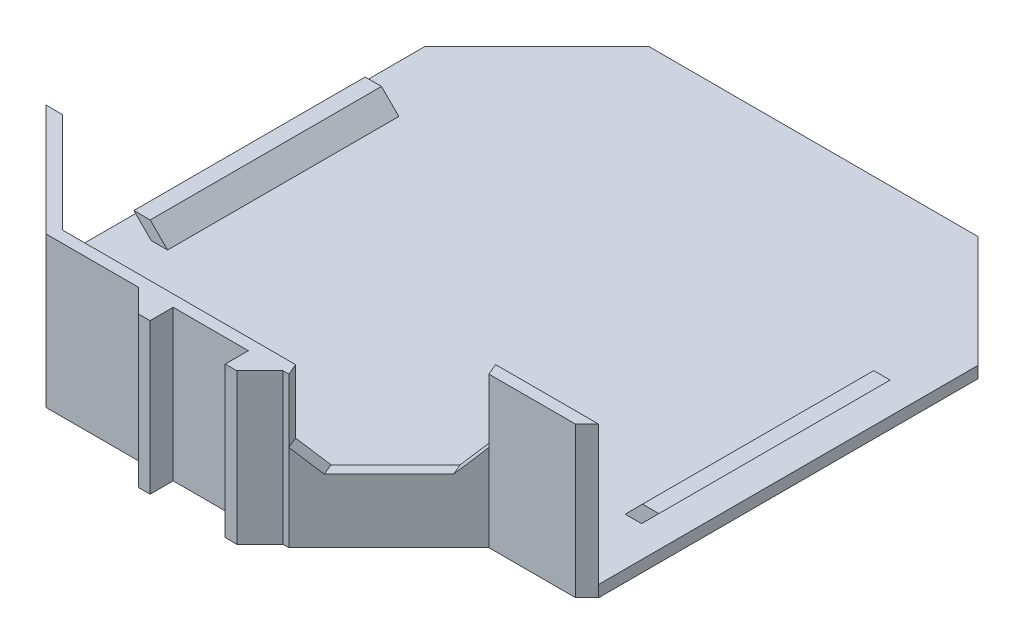
SolidWorks part; units mm, degrees
ref_plane "Front Plane" through (0, 0, 0) normal (0, 0, 1) x (1, 0, 0)
ref_plane "Top Plane" through (0, 0, 0) normal (0, 1, 0) x (1, 0, 0)
ref_plane "Right Plane" through (0, 0, 0) normal (1, 0, 0) x (0, 0, -1)
sketch "Sketch1" plane through (0, 0, 0) normal (0, 1, 0) x (1, 0, 0)
  line L0 (-1145.7751, 0) -> (48854.2249, 0) construction
  line L1 (0, -935.409) -> (0, 49064.591) construction
  line L2 (-36.195, 66.167) -> (36.195, 66.167)
  line L3 (36.195, 66.167) -> (60.706, 41.656)
  line L4 (60.706, 41.656) -> (60.706, -41.656)
  line L5 (-60.706, 41.656) -> (-60.706, -41.656)
  line L6 (-36.195, 66.167) -> (-60.706, 41.656)
  line L7 (-36.195, -66.167) -> (-60.706, -41.656)
  line L8 (-36.195, -66.167) -> (36.195, -66.167)
  line L9 (36.195, -66.167) -> (60.706, -41.656)
  point P10 (0, 66.167)
  point P11 (-60.706, 0)
  point P14 (60.706, 0)
  dimension "D1" = 132.334
  dimension "D2" = 121.412
  dimension "D3" = 135
  dimension "D4" = 41.656
extrude "Boss-Extrude1" add sketch "Sketch1" along normal blind 2.54
sketch "Sketch5" plane through (0, 2.54, 0) normal (0, 1, 0) x (1, 0, 0)
  line L0 (58.166, -44.196) -> (36.195, -66.167)
  line L1 (36.195, -66.167) -> (60.706, -41.656) construction
  line L2 (36.195, -66.167) -> (17.145, -66.167)
  line L3 (-36.195, -66.167) -> (36.195, -66.167) construction
  line L4 (17.145, -66.167) -> (39.116, -44.196)
  line L5 (39.116, -44.196) -> (58.166, -44.196)
  dimension "D1" = 19.05
  dimension "D2" = 2.54
extrude "Cut-Extrude1" cut sketch "Sketch5" against normal through all
sketch "Case Reference" plane through (0, 0, 0) normal (0, 0, 1) x (1, 0, 0)
  line L0 (-60.706, 2.54) -> (-60.706, 13.97) construction
  line L1 (-60.706, 13.97) -> (-58.166, 13.97) construction
  line L2 (-58.166, 13.97) -> (-58.166, 6.35) construction
  line L3 (-58.166, 6.35) -> (-54.356, 2.54) construction
  line L4 (-60.706, 2.54) -> (-36.195, 2.54) construction
  line L5 (-54.356, 2.54) -> (-60.706, 2.54) construction
  line L6 (0, -1000) -> (0, 49000) construction
  line L7 (54.356, 2.54) -> (60.706, 2.54) construction
  line L8 (58.166, 6.35) -> (54.356, 2.54) construction
  line L9 (58.166, 13.97) -> (58.166, 6.35) construction
  line L10 (60.706, 13.97) -> (58.166, 13.97) construction
  line L11 (60.706, 2.54) -> (60.706, 13.97) construction
  dimension "D1" = 3.81
  dimension "D2" = 2.54
  dimension "D3" = 45
  dimension "D4" = 7.62
sketch "Sketch3" plane through (0, 0, 0) normal (0, 0, 1) x (1, 0, 0)
  line L0 (-53.848, 2.54) -> (-57.658, 6.35)
  line L1 (-60.706, 2.54) -> (-36.195, 2.54) construction
  line L2 (-57.658, 6.35) -> (-54.0659, 6.35)
  line L3 (-54.0659, 6.35) -> (-50.2559, 2.54)
  line L4 (-50.2559, 2.54) -> (-53.848, 2.54)
  line L7 (0, -201000) -> (0, 249000) construction
  line L8 (0, -201000) -> (0, 249000)
  line L9 (54.0659, 6.35) -> (50.2559, 2.54)
  line L10 (57.658, 6.35) -> (54.0659, 6.35)
  line L11 (53.848, 2.54) -> (57.658, 6.35)
  line L12 (50.2559, 2.54) -> (53.848, 2.54)
  dimension "D1" = 45
  dimension "D2" = 0.508
  dimension "D3" = 2.54
extrude "Boss-Extrude2" add sketch "Sketch3" along normal blind 25.4 and the other way blind 25.4
sketch "Sketch4" plane through (0, 2.54, 0) normal (0, 1, 0) x (1, 0, 0)
  line L4 (60.706, -41.656) -> (58.166, -41.656)
  line L6 (58.166, -44.196) -> (60.706, -41.656) construction
  line L21 (58.166, -44.196) -> (39.116, -44.196) construction
  line L22 (39.116, -44.196) -> (17.145, -66.167) construction
  line L28 (-36.195, -66.167) -> (17.145, -66.167) construction
  line L29 (-60.706, -41.656) -> (-36.195, -66.167) construction
  line L30 (58.166, -44.196) -> (60.706, -41.656)
  line L31 (58.166, -44.196) -> (39.116, -44.196)
  line L32 (39.116, -44.196) -> (17.145, -66.167)
  line L33 (-36.195, -66.167) -> (17.145, -66.167)
  line L34 (-60.706, -41.656) -> (-36.195, -66.167)
  line L35 (-57.1139, -41.656) -> (-35.1429, -63.627)
  line L36 (-35.1429, -63.627) -> (16.0929, -63.627)
  line L37 (38.0639, -41.656) -> (16.0929, -63.627)
  line L38 (58.166, -41.656) -> (38.0639, -41.656)
  line L39 (-60.706, -41.656) -> (-57.1139, -41.656)
  line L40 (-58.9099, -39.8599) -> (-35.1429, -63.627) construction
  dimension "D1" = 2.54
extrude "Boss-Extrude3" add sketch "Sketch4" along normal blind 30.48
sketch "Sketch6" plane through (0, 33.02, 0) normal (0, 1, 0) x (1, 0, 0)
  line L0 (38.0639, -41.656) -> (16.0929, -63.627) construction
  line L1 (17.145, -66.167) -> (39.116, -44.196) construction
  line L2 (38.0639, -41.656) -> (16.0929, -63.627)
  line L3 (17.145, -66.167) -> (39.116, -44.196)
  line L4 (17.145, -66.167) -> (16.0929, -63.627)
  line L5 (39.116, -44.196) -> (38.0639, -41.656)
extrude "Cut-Extrude2" cut sketch "Sketch6" against normal blind 19.05
chamfer "Chamfer2" distance 5.08 angle 45 2 edges at (16.6189, 13.97, 64.897) (38.5899, 13.97, 42.926)
sketch "Sketch7" plane through (0, 0, 0) normal (0, -1, 0) x (1, 0, 0)
  line L0 (0, -1000) -> (0, 49000) construction
  line L1 (-8.255, 66.167) -> (-8.255, 71.247)
  line L2 (-36.195, 66.167) -> (17.145, 66.167) construction
  line L3 (-8.255, 71.247) -> (-10.795, 71.247)
  line L4 (-10.795, 71.247) -> (-15.875, 66.167)
  line L5 (-15.875, 66.167) -> (-8.255, 66.167)
  line L6 (10.795, 71.247) -> (15.875, 66.167)
  line L7 (8.255, 71.247) -> (10.795, 71.247)
  line L8 (8.255, 66.167) -> (8.255, 71.247)
  line L9 (15.875, 66.167) -> (8.255, 66.167)
  dimension "D1" = 16.51
  dimension "D2" = 2.54
  dimension "D3" = 45
  dimension "D4" = 5.08
extrude "Boss-Extrude4" add sketch "Sketch7" against normal up to surface (33.02 mm away) up to face at (49.013, 33.02, 42.926)
